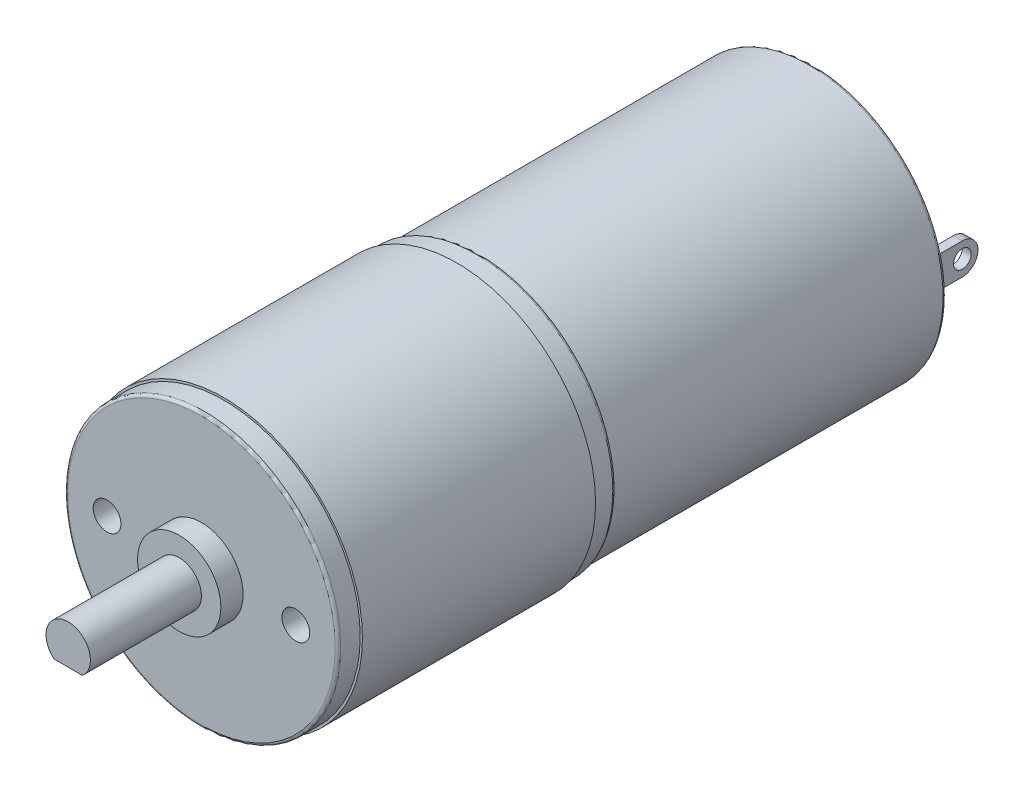
SolidWorks part; units mm, degrees
material "6061-T6 (SS)"
ref_plane "Front Plane" through (0, 0, 0) normal (0, 0, 1) x (1, 0, 0)
ref_plane "Top Plane" through (0, 0, 0) normal (0, 1, 0) x (1, 0, 0)
ref_plane "Right Plane" through (0, 0, 0) normal (1, 0, 0) x (0, 0, -1)
sketch "Sketch1" plane through (0, 0, 0) normal (0, 0, 1) x (1, 0, 0)
  circle A0 centre (0, 0) radius 12.3
extrude "Boss-Extrude1" add sketch "Sketch1" along normal blind 2
fillet "Fillet1" radius 0.25 1 edges at (12.3, 0, 2)
sketch "Sketch3" plane through (0, 0, 0) normal (0, 0, -1) x (-1, 0, 0)
  circle A0 centre (0, 0) radius 12.5
extrude "Boss-Extrude3" add sketch "Sketch3" along normal blind 21
sketch "Sketch4" plane through (0, 0, -21) normal (0, 0, -1) x (-1, 0, 0)
  circle A0 centre (0, 0) radius 12.3
extrude "Boss-Extrude4" add sketch "Sketch4" along normal blind 2
fillet "Fillet3" radius 0.25 1 edges at (-12.3, 0, -23)
sketch "Sketch5" plane through (0, 0, -23) normal (0, 0, -1) x (-1, 0, 0)
  circle A0 centre (0, 0) radius 12.05
extrude "Boss-Extrude5" add sketch "Sketch5" along normal blind 30
fillet "Fillet4" radius 0.25 1 edges at (-12.05, 0, -53)
sketch "Sketch6" plane through (0, 0, -53) normal (0, 0, -1) x (-1, 0, 0)
  line L0 (0, 8.7019) -> (0, -7.9452) construction
  line L1 (-10.0892, 1.5386) -> (-9.282, 1.5386)
  line L2 (-10.0892, 1.5386) -> (-10.0892, -1.2864)
  line L3 (-10.0892, -1.2864) -> (-9.282, -1.2864)
  line L4 (-9.282, 1.5386) -> (-9.282, -1.2864)
  line L5 (9.282, 1.5386) -> (9.282, -1.2864)
  line L6 (10.0892, -1.2864) -> (9.282, -1.2864)
  line L7 (10.0892, 1.5386) -> (10.0892, -1.2864)
  line L8 (10.0892, 1.5386) -> (9.282, 1.5386)
extrude "Boss-Extrude6" add sketch "Sketch6" along normal blind 5
sketch "Sketch7" plane through (10.0892, 0, 0) normal (1, 0, 0) x (0, 0, -1)
  line L0 (58, 1.5386) -> (53, 1.5386) construction
  line L1 (58, -1.2864) -> (53, -1.2864) construction
  line L2 (56.4393, 1.5386) -> (58, 1.5386)
  line L3 (58, 1.5386) -> (58, -1.2864)
  line L4 (58, -1.2864) -> (56.4393, -1.2864)
  circle A0 centre (56.4393, 0.1261) radius 0.8
  arc A1 (56.4393, 1.5386) -> (56.4393, -1.2864) centre (56.4393, 0.1261) cw
extrude "Cut-Extrude1" cut sketch "Sketch7" against normal through all
sketch "Sketch8" plane through (0, 0, -53) normal (0, 0, -1) x (-1, 0, 0)
  circle A0 centre (0, 0) radius 2.5
extrude "Boss-Extrude7" add sketch "Sketch8" along normal blind 0.5
sketch "Sketch9" plane through (0, 0, 2) normal (0, 0, 1) x (1, 0, 0)
  circle A0 centre (0, 0) radius 3.75
extrude "Boss-Extrude8" add sketch "Sketch9" along normal blind 2
sketch "Sketch10" plane through (0, 0, 4) normal (0, 0, 1) x (1, 0, 0)
  line L0 (-1.2883, -1.5298) -> (1.2622, -1.5514)
  arc A0 (1.2622, -1.5514) -> (-1.2883, -1.5298) centre (0, 0) ccw
extrude "Boss-Extrude9" add sketch "Sketch10" along normal blind 10
hole_wizard "Tap Drill for M3x0.5 Tap1" positions "Sketch12" profile "Sketch11" hole size "M3x0.5" standard "ANSI Metric"
sketch "Sketch12" plane through (0, 0, 2) normal (0, 0, 1) x (1, 0, 0)
  point P0 (8.5, 0)
  point P2 (-8.5, 0)
  dimension "D1" = 8.5
  dimension "D2" = 8.5
sketch "Sketch11" plane through (8.5, 0, 2) normal (1, 0, 0) x (0, -1, 0)
  line L0 (0, 0) -> (0, 10)
  line L1 (0, 10) -> (1.25, 10)
  line L2 (1.25, 10) -> (1.25, 0)
  line L5 (1.25, 0) -> (0, 0)
  line L10 (0, 10) -> (-1.25, 10) construction
  line L11 (0, -6.35) -> (0, 107.95) construction
  dimension "Hole Dia." = 2.5
  dimension "Hole Depth" = 10
  dimension "Drill Angle" = 180
sketch "Sketch13" plane through (0, 0, 14) normal (0, 0, 1) x (1, 0, 0)
  line L0 (-0.013, -1.5406) -> (0.0169, 1.9999) construction
  line L1 (-1.2883, -1.5298) -> (1.2622, -1.5514) construction
  arc A0 (1.2622, -1.5514) -> (-1.2883, -1.5298) centre (0, 0) ccw construction
